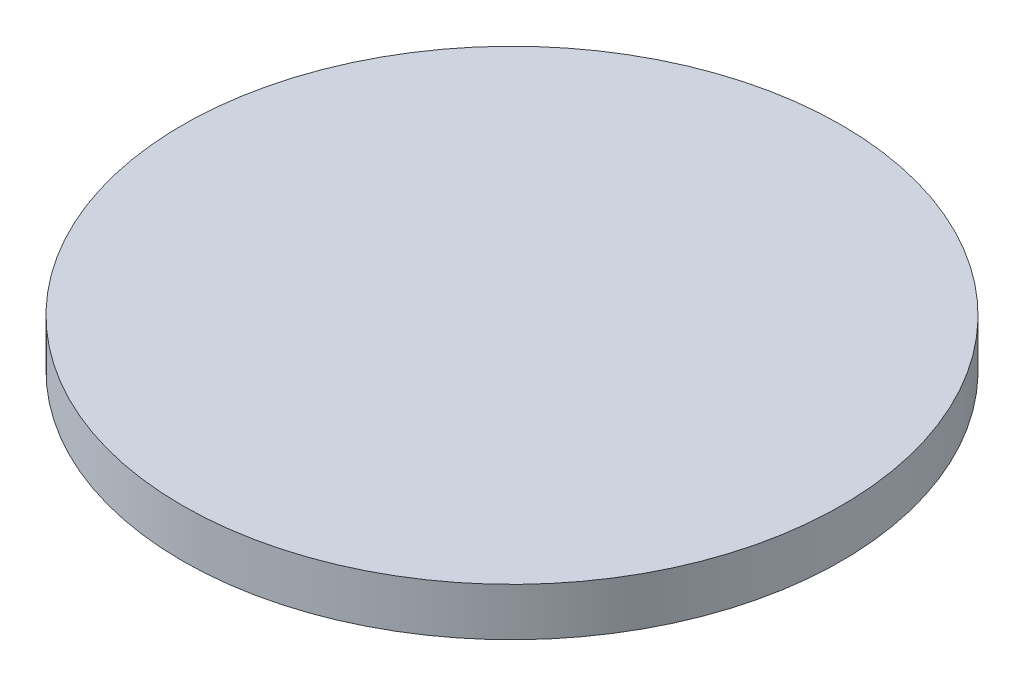
SolidWorks part; units mm, degrees
ref_plane "Front Plane" through (0, 0, 0) normal (0, 0, 1) x (1, 0, 0)
ref_plane "Top Plane" through (0, 0, 0) normal (0, 1, 0) x (1, 0, 0)
ref_plane "Right Plane" through (0, 0, 0) normal (1, 0, 0) x (0, 0, -1)
sketch "Sketch1" plane through (0, 14.4783, 0) normal (0, -1, 0) x (1, 0, 0)
  circle A0 centre (91.8165, 48.1631) radius 17.45
extrude "Boss-Extrude1" add sketch "Sketch1" along normal blind 2.54
